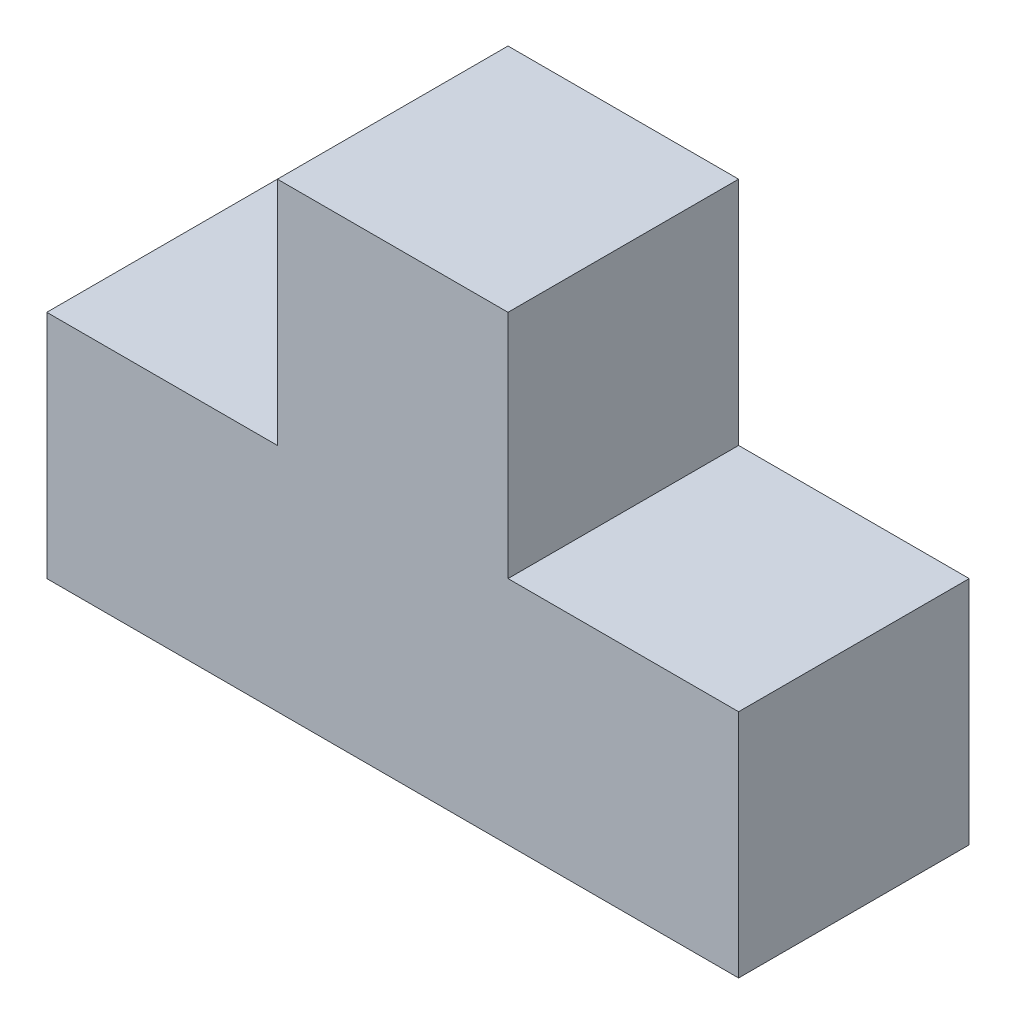
SolidWorks part; units mm, degrees
ref_plane "Front Plane" through (0, 0, 0) normal (0, 0, 1) x (1, 0, 0)
ref_plane "Top Plane" through (0, 0, 0) normal (0, 1, 0) x (1, 0, 0)
ref_plane "Right Plane" through (0, 0, 0) normal (1, 0, 0) x (0, 0, -1)
sketch "Sketch1" plane through (0, 0, 0) normal (0, 0, 1) x (1, 0, 0)
  line L0 (-103.4966, 0) -> (89.7361, 0) construction
  line L1 (0, 78.5443) -> (0, -48.8471) construction
  line L10 (-45, 0) -> (45, 0)
  line L11 (45, 0) -> (45, 30)
  line L12 (45, 30) -> (15, 30)
  line L13 (15, 30) -> (15, 60)
  line L14 (15, 60) -> (-15, 60)
  line L15 (-15, 60) -> (-15, 30)
  line L16 (-15, 30) -> (-45, 30)
  line L17 (-45, 30) -> (-45, 0)
  dimension "D1" = 60
  dimension "D2" = 30
  dimension "D3" = 90
  dimension "D4" = 30
  dimension "D5" = 30
extrude "Boss-Extrude1" add sketch "Sketch1" against normal blind 30
